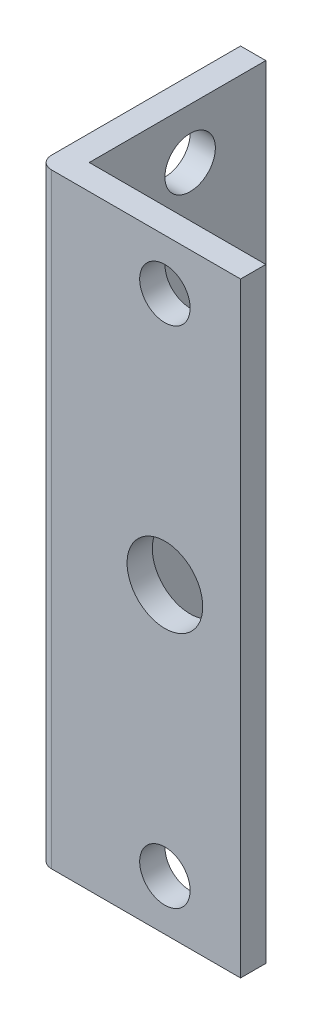
SolidWorks part; units mm, degrees
ref_plane "Front Plane" through (0, 0, 0) normal (0, 0, 1) x (1, 0, 0)
ref_plane "Top Plane" through (0, 0, 0) normal (0, 1, 0) x (1, 0, 0)
ref_plane "Right Plane" through (0, 0, 0) normal (1, 0, 0) x (0, 0, -1)
ref_plane "Plane1" through (-13.9843, 0, 0) normal (-1, 0, 0) x (0, -1, 0)
sketch "Sketch1" plane through (-13.9843, 0, 0) normal (-1, 0, 0) x (0, -1, 0)
  line L0 (38.1, -13.288) -> (38.1, 12.112)
  line L1 (38.1, 12.112) -> (-38.1, 12.112)
  line L2 (-38.1, 12.112) -> (-38.1, -13.288)
  line L3 (-38.1, -13.288) -> (38.1, -13.288)
extrude "Boss-Extrude1" add sketch "Sketch1" against normal blind 25.4
sketch "Sketch2" plane through (0, -38.1, 0) normal (0, -1, 0) x (1, 0, 0)
  line L0 (11.4157, 8.937) -> (-10.8093, 8.937)
  line L1 (-10.8093, 8.937) -> (-10.8093, -13.288)
  line L2 (-10.8093, -13.288) -> (11.4157, -13.288)
  line L3 (11.4157, -13.288) -> (11.4157, 8.937)
extrude "Cut-Extrude1" cut sketch "Sketch2" against normal through all
fillet "Fillet1" radius 1.5875 1 edges at (-13.9843, 0, 12.112)
sketch "Sketch7" plane through (0, 0, 12.112) normal (0, 0, 1) x (1, 0, 0)
  line L0 (11.4157, 0) -> (1.8907, 0)
  line L1 (11.4157, -38.1) -> (11.4157, 38.1) construction
  line L2 (1.8907, 0) -> (1.8907, 35.1156)
  point P5 (1.8907, 31.75)
  point P6 (1.8907, -31.75)
  point P7 (0, 0)
  point P9 (1.8907, 31.75)
  point P10 (1.8907, -31.75)
  dimension "D1" = 9.525
  dimension "D2" = 31.75
  dimension "D3" = 31.75
sketch "Sketch8" plane through (-13.9843, 0, 0) normal (-1, 0, 0) x (0, 0, 1)
  line L0 (-13.288, 0) -> (-3.763, 0)
  line L1 (-13.288, 38.1) -> (-13.288, -38.1) construction
  point P5 (-3.763, 31.75)
  point P6 (-3.763, -31.75)
  point P7 (-3.763, 31.75)
  point P8 (-3.763, 0)
  dimension "D1" = 9.525
  dimension "D2" = 31.75
  dimension "D3" = 31.75
hole_wizard "1/4 (0.25) Diameter Hole4" positions "3DSketch4" profile "Sketch12" hole size "1/4" standard "ANSI Inch" end condition up to next
sketch3d "3DSketch4"
  point P0 (1.8907, 31.75, 12.112)
  point P3 (1.8907, -31.75, 12.112)
  point P6 (-13.9843, 31.75, -3.763)
  point P9 (-13.9843, -31.75, -3.763)
sketch "Sketch12" plane through (1.8907, 31.75, 12.112) normal (1, 0, 0) x (0, -1, 0)
  line L0 (0, 0) -> (0, 3.175)
  line L1 (0, 3.175) -> (3.175, 3.175)
  line L2 (3.175, 3.175) -> (3.175, 0)
  line L5 (3.175, 0) -> (0, 0)
  line L11 (0, -6.35) -> (0, 107.95) construction
  dimension "Thru Hole Dia." = 6.35
  dimension "Thru Hole Depth" = 3.175
hole_wizard "3/8 (0.375) Diameter Hole1" positions "3DSketch5" profile "Sketch13" hole size "3/8" standard "ANSI Inch" end condition through all
sketch3d "3DSketch5"
  point P0 (-13.9843, 0, -3.763)
  point P3 (1.8907, 0, 12.112)
sketch "Sketch13" plane through (-13.9843, 0, -3.763) normal (0, 1, 0) x (0, 0, 1)
  line L0 (0, 0) -> (0, 25.4)
  line L1 (0, 25.4) -> (4.7625, 25.4)
  line L2 (4.7625, 25.4) -> (4.7625, 0)
  line L5 (4.7625, 0) -> (0, 0)
  line L11 (0, -6.35) -> (0, 107.95) construction
  dimension "Thru Hole Dia." = 9.525
  dimension "Thru Hole Depth" = 25.4
